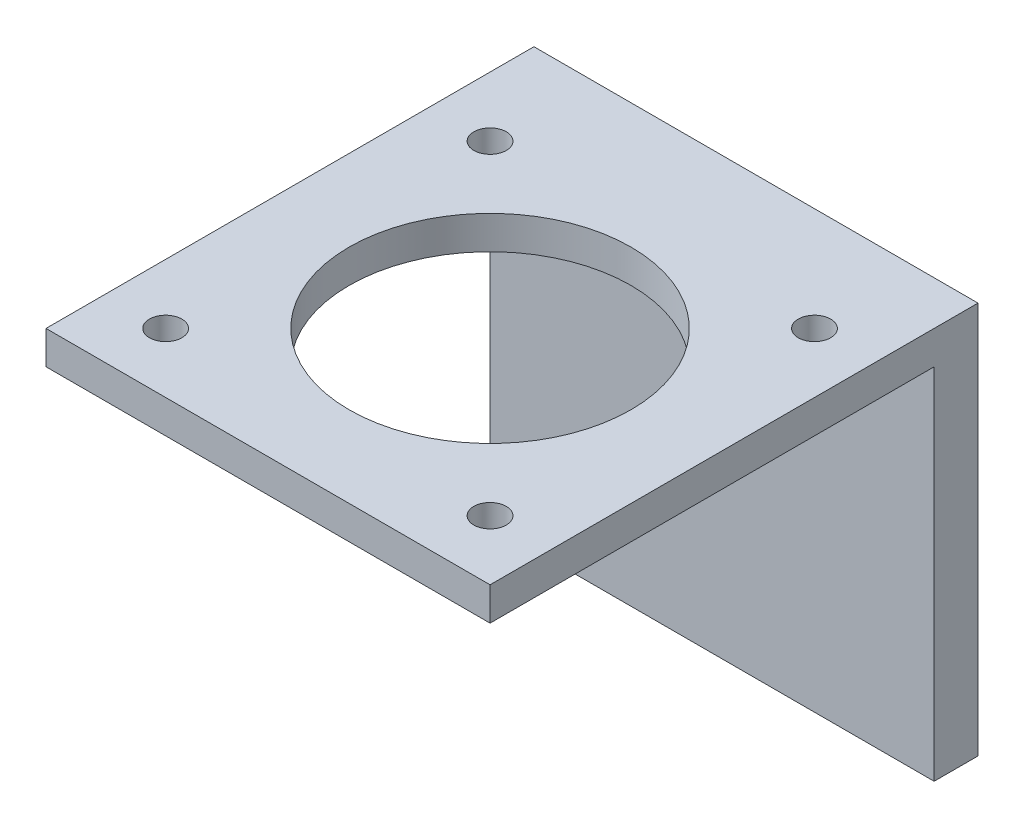
SolidWorks part; units mm, degrees
material "6061-T6 (SS)"
ref_plane "Front Plane" through (0, 0, 0) normal (0, 0, 1) x (1, 0, 0)
ref_plane "Top Plane" through (0, 0, 0) normal (0, 1, 0) x (1, 0, 0)
ref_plane "Right Plane" through (0, 0, 0) normal (1, 0, 0) x (0, 0, -1)
sketch "Sketch1" plane through (0, 0, 0) normal (0, 1, 0) x (1, 0, 0)
  line L0 (0, 0) -> (0, 45.9087) construction
  line L1 (-21.209, -21.209) -> (21.209, -21.209)
  line L2 (-21.209, -21.209) -> (-21.209, 21.209)
  line L3 (-21.209, 21.209) -> (21.209, 21.209)
  line L4 (21.209, -21.209) -> (21.209, 21.209)
  line L5 (-21.209, -21.209) -> (21.209, 21.209) construction
  line L6 (-21.209, 21.209) -> (21.209, -21.209) construction
  line L7 (0, 0) -> (42.3888, 0) construction
  circle A0 centre (15.494, 15.494) radius 1.5494
  circle A1 centre (-15.494, 15.494) radius 1.5494
  circle A2 centre (15.494, -15.494) radius 1.5494
  circle A3 centre (-15.494, -15.494) radius 1.5494
  circle A4 centre (0, 0) radius 13.462
  point P0 (0, 0)
  dimension "D2" = 3.0988
  dimension "D4" = 5.715
  dimension "D5" = 26.924
  dimension "D1" = 42.418
  dimension "D3" = 5.715
extrude "Boss-Extrude1" add sketch "Sketch1" along normal blind 3.175
sketch "Sketch3" plane through (0, 3.175, 0) normal (0, 1, 0) x (1, 0, 0)
  line L0 (-21.209, 21.209) -> (-21.209, 25.4)
  line L1 (-21.209, 25.4) -> (21.209, 25.4)
  line L2 (21.209, 21.209) -> (21.209, 25.4)
  line L3 (-21.209, 21.209) -> (21.209, 21.209)
  dimension "D1" = 4.191
extrude "Boss-Extrude2" add sketch "Sketch3" against normal blind 37.465
